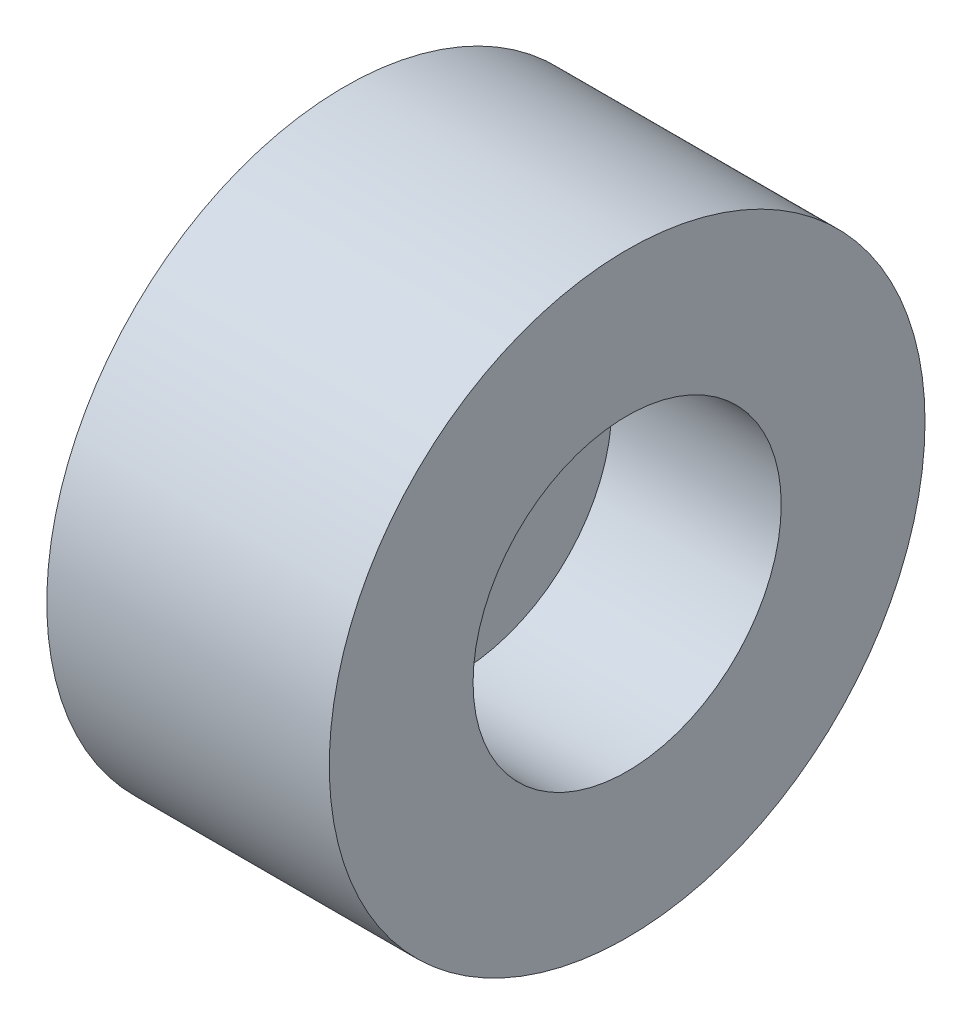
SolidWorks part; units mm, degrees
ref_plane "Front Plane" through (0, 0, 0) normal (0, 0, 1) x (1, 0, 0)
ref_plane "Top Plane" through (0, 0, 0) normal (0, 1, 0) x (1, 0, 0)
ref_plane "Right Plane" through (0, 0, 0) normal (1, 0, 0) x (0, 0, -1)
sketch "Sketch1" plane through (0, 0, 0) normal (1, 0, 0) x (0, 0, -1)
  circle A0 centre (0, 0) radius 5.8
extrude "Boss-Extrude1" add sketch "Sketch1" along normal blind 5.5
sketch "Sketch2" plane through (5.5, 0, 0) normal (1, 0, 0) x (0, 0, -1)
  circle A0 centre (0, 0) radius 3
extrude "Cut-Extrude1" cut sketch "Sketch2" against normal blind 3.3
sketch "Sketch3" plane through (2.2, 0, 0) normal (1, 0, 0) x (0, 0, -1)
  circle A0 centre (0, 0) radius 1.5
extrude "Cut-Extrude2" cut sketch "Sketch3" against normal blind 3.3
